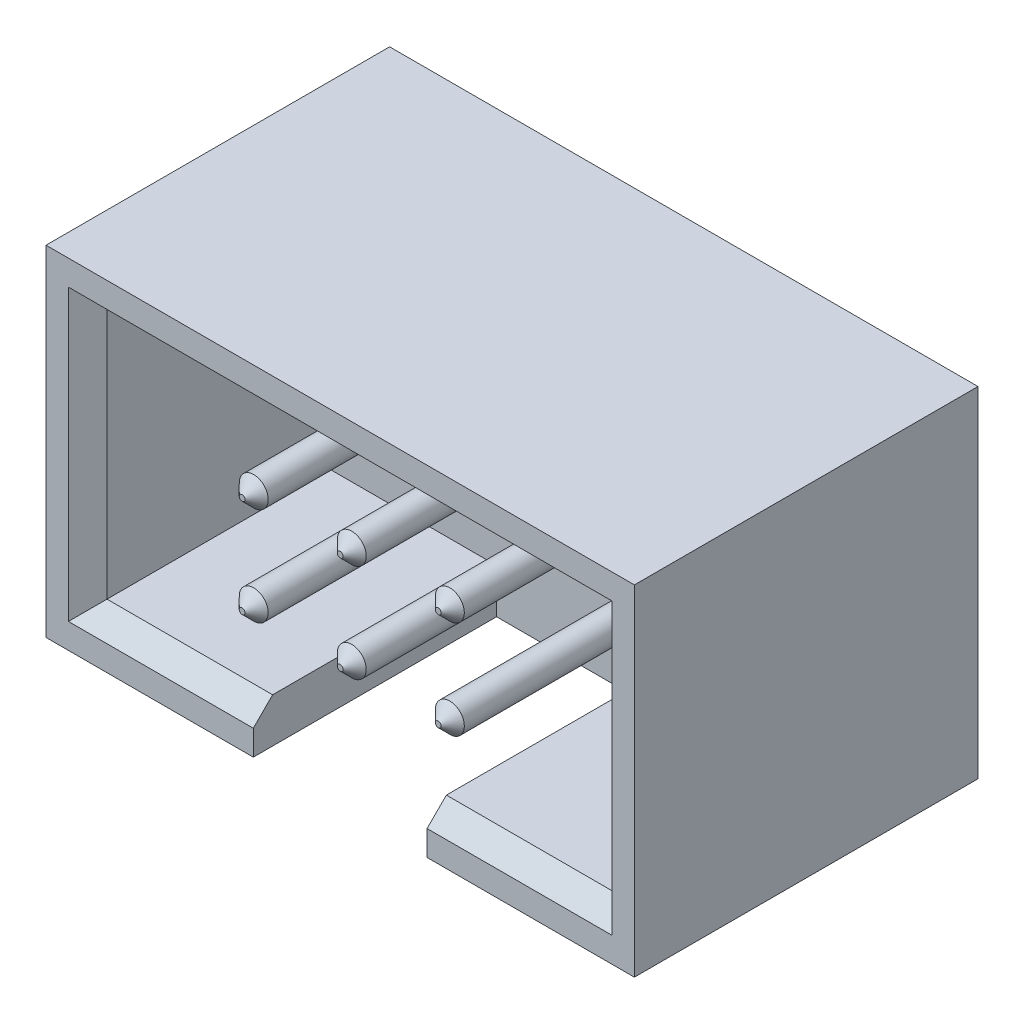
SolidWorks part; units mm, degrees
ref_plane "Front Plane" through (0, 0, 0) normal (0, 0, 1) x (1, 0, 0)
ref_plane "Top Plane" through (0, 0, 0) normal (0, 1, 0) x (1, 0, 0)
ref_plane "Right Plane" through (0, 0, 0) normal (1, 0, 0) x (0, 0, -1)
sketch "Sketch1" plane through (0, 0, 0) normal (0, 0, 1) x (1, 0, 0)
  line L1 (-7.62, 4.4) -> (7.62, 4.4)
  line L2 (-7.62, 4.4) -> (-7.62, -4.4)
  line L3 (-7.62, -4.4) -> (7.62, -4.4)
  line L4 (7.62, 4.4) -> (7.62, -4.4)
  line L5 (-7.62, 4.4) -> (7.62, -4.4) construction
  line L6 (-7.62, -4.4) -> (7.62, 4.4) construction
  point P0 (0, 0)
extrude "Boss-Extrude1" add sketch "Sketch1" along normal blind 2.6
sketch "Sketch2" plane through (0, 0, 2.6) normal (0, 0, 1) x (1, 0, 0)
  line L1 (-6.54, 3.25) -> (6.54, 3.25)
  line L2 (-6.54, 3.25) -> (-6.54, -3.25)
  line L3 (-6.54, -3.25) -> (-2.25, -3.25)
  line L4 (6.54, 3.25) -> (6.54, -3.25)
  line L5 (-6.54, 3.25) -> (6.54, -3.25) construction
  line L6 (-6.54, -3.25) -> (6.54, 3.25) construction
  line L7 (2.25, -3.25) -> (2.25, -4.4)
  line L8 (-2.25, -3.25) -> (-2.25, -4.4)
  line L9 (2.25, -3.25) -> (6.54, -3.25)
  line L10 (7.62, -4.4) -> (7.62, 4.4)
  line L11 (7.62, 4.4) -> (-7.62, 4.4)
  line L12 (-7.62, 4.4) -> (-7.62, -4.4)
  line L13 (-7.62, -4.4) -> (7.62, -4.4)
  line L14 (7.62, -4.4) -> (7.62, 4.4)
  line L15 (7.62, 4.4) -> (-7.62, 4.4)
  line L16 (-7.62, 4.4) -> (-7.62, -4.4)
  line L17 (-7.62, -4.4) -> (-2.25, -4.4)
  line L18 (2.25, -4.4) -> (7.62, -4.4)
  point P0 (0, 0)
  dimension "D1" = 0
extrude "Boss-Extrude2" add sketch "Sketch2" along normal blind 6.3
chamfer "Chamfer1" distance 0.5 angle 45 5 edges at (-4.395, -3.25, 8.9) (4.395, -3.25, 8.9) (6.54, 0, 8.9) (-6.54, 0, 8.9) (0, 3.25, 8.9)
sketch "Sketch3" plane through (0, 0, 2.6) normal (0, 0, 1) x (1, 0, 0)
  line L0 (-0.8423, 0) -> (0.8144, 0) construction
  circle A0 centre (0, 1.27) radius 0.4
  circle A1 centre (2.54, 1.27) radius 0.4
  circle A2 centre (-2.54, 1.27) radius 0.4
  circle A3 centre (2.54, -1.27) radius 0.4
  circle A4 centre (0, -1.27) radius 0.4
  circle A5 centre (-2.54, -1.27) radius 0.4
  point P0 (0, 0)
  dimension "D1" = 1.27
  dimension "D2" = 1.27
  dimension "D3" = 1.27
  dimension "D4" = 2.54
  dimension "D5" = 2.54
  dimension "D6" = 2.54
extrude "Cut-Extrude1" cut sketch "Sketch3" against normal up to next
sketch "Sketch4" plane through (0, 0, 2.6) normal (0, 0, 1) x (1, 0, 0)
  circle A0 centre (-2.54, 1.27) radius 0.375
  circle A1 centre (0, 1.27) radius 0.375
  circle A2 centre (2.54, 1.27) radius 0.375
  circle A3 centre (-2.54, -1.27) radius 0.375
  circle A4 centre (0, -1.27) radius 0.375
  circle A5 centre (2.54, -1.27) radius 0.375
extrude "Boss-Extrude3" add sketch "Sketch4" along normal blind 6.3 and the other way blind 5.4 separate body
chamfer "Chamfer2" distance 0.3 1 edges at (-2.165, -1.27, 8.9)
chamfer "Chamfer3" distance 0.3 angle 45 1 edges at (-2.165, -1.27, -2.8)
chamfer "Chamfer4" distance 0.3 angle 45 1 edges at (0.375, -1.27, -2.8)
chamfer "Chamfer5" distance 0.3 angle 45 2 edges at (2.915, -1.27, 8.9) (2.915, -1.27, -2.8)
chamfer "Chamfer6" distance 0.3 angle 45 1 edges at (2.915, 1.27, -2.8)
chamfer "Chamfer7" distance 0.3 angle 45 1 edges at (0.375, 1.27, -2.8)
chamfer "Chamfer8" distance 0.3 angle 45 1 edges at (-2.165, 1.27, -2.8)
chamfer "Chamfer9" distance 0.3 angle 45 1 edges at (0.375, -1.27, 8.9)
chamfer "Chamfer10" distance 0.3 angle 45 1 edges at (2.915, 1.27, 8.9)
chamfer "Chamfer11" distance 0.3 angle 45 1 edges at (0.375, 1.27, 8.9)
chamfer "Chamfer12" distance 0.3 angle 45 1 edges at (-2.165, 1.27, 8.9)
